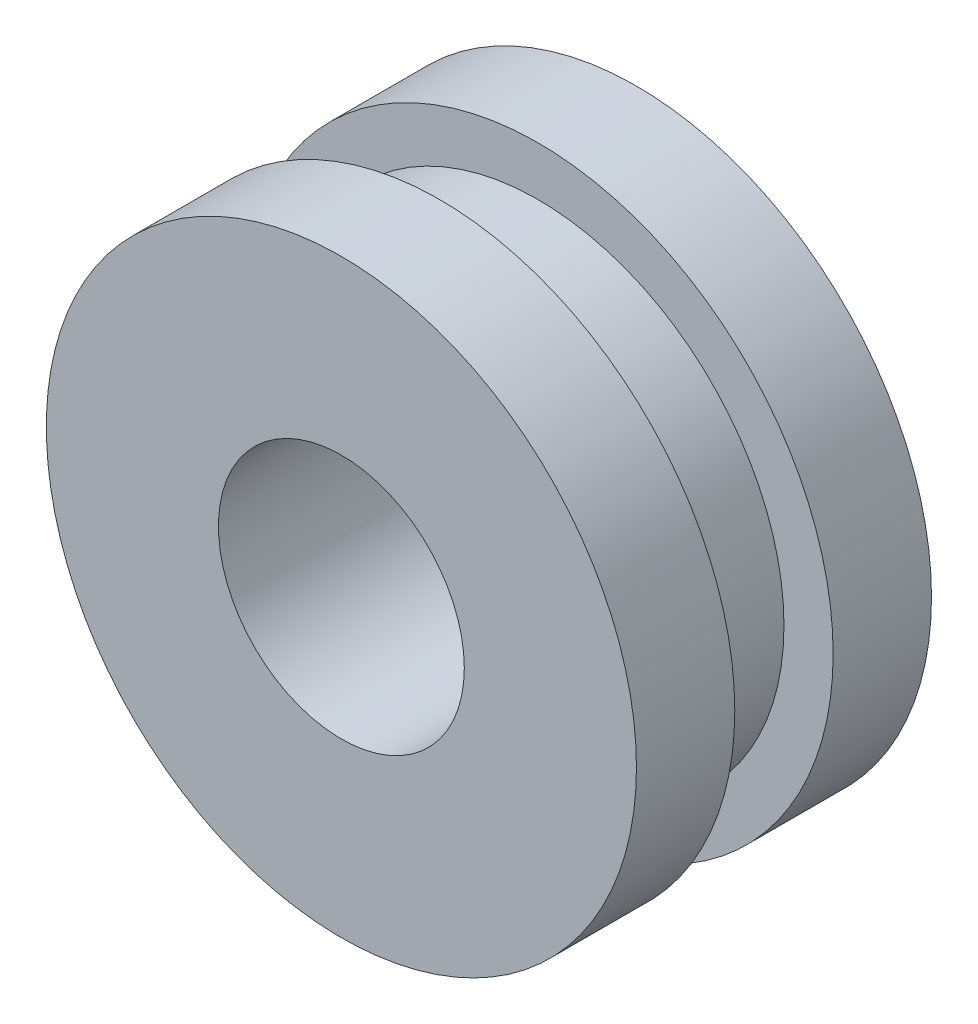
SolidWorks part; units mm, degrees
ref_plane "Front Plane" through (0, 0, 0) normal (0, 0, 1) x (1, 0, 0)
ref_plane "Top Plane" through (0, 0, 0) normal (0, 1, 0) x (1, 0, 0)
ref_plane "Right Plane" through (0, 0, 0) normal (1, 0, 0) x (0, 0, -1)
sketch "Sketch1" plane through (0, 0, 0) normal (0, 0, 1) x (1, 0, 0)
  circle A0 centre (0, 0) radius 7.62
  dimension "D1" = 15.24
extrude "Boss-Extrude1" add sketch "Sketch1" along normal blind 2.54
sketch "Sketch2" plane through (0, 0, 2.54) normal (0, 0, 1) x (1, 0, 0)
  circle A0 centre (0, 0) radius 6.35
  dimension "D1" = 12.7
extrude "Boss-Extrude2" add sketch "Sketch2" along normal blind 2.54
ref_plane "Plane1" through (0, 0, 3.81) normal (0, 0, 1) x (1, 0, 0)
mirror "Mirror1" about plane through (0, 0, 3.81) normal (0, 0, 1) of "Boss-Extrude1"
sketch "Sketch4" plane through (0, 0, 7.62) normal (0, 0, 1) x (1, 0, 0)
  circle A0 centre (0, 0) radius 3.175
  dimension "D1" = 6.35
extrude "Cut-Extrude1" cut sketch "Sketch4" against normal through all
